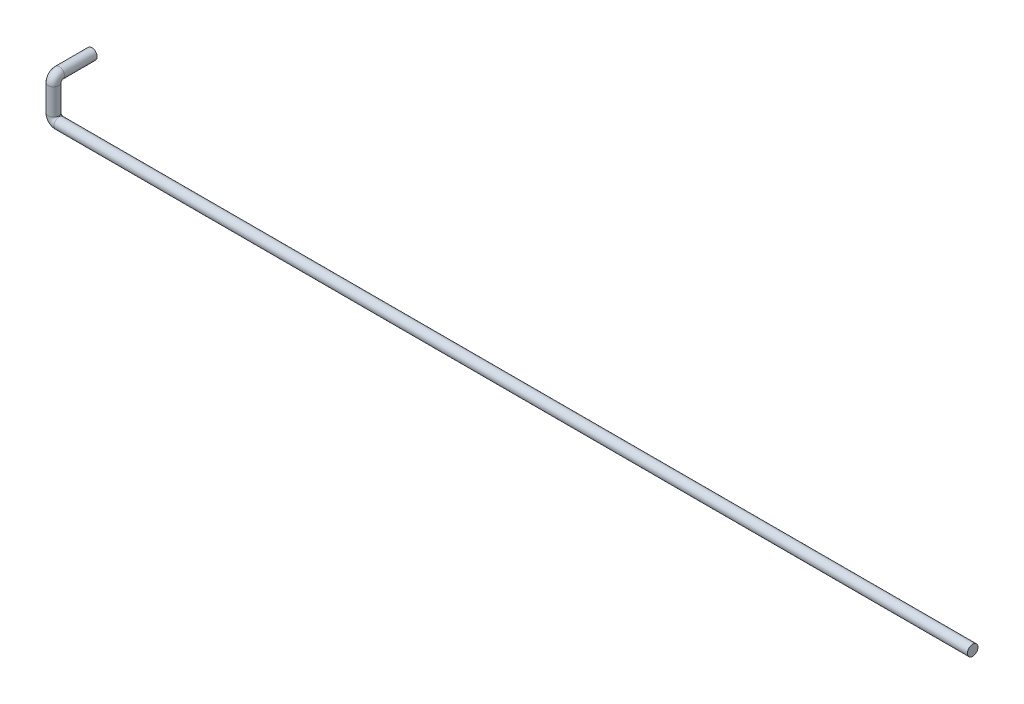
SolidWorks part; units mm, degrees
ref_plane "Alzado" through (0, 0, 0) normal (0, 0, 1) x (1, 0, 0)
ref_plane "Planta" through (0, 0, 0) normal (0, 1, 0) x (1, 0, 0)
ref_plane "Vista lateral" through (0, 0, 0) normal (1, 0, 0) x (0, 0, -1)
sketch3d "Croquis3D1"
  line L0 (0, 0, 0) -> (-2374, 0, 0)
  line L1 (-2389, 15, 0) -> (-2389, 83, 0)
  line L2 (-2389, 98, -15) -> (-2389, 98, -100)
  arc A0 (-2389, 83, 0) -> (-2389, 98, -15) centre (-2389, 83, -15) ccw
  arc A1 (-2374, 0, 0) -> (-2389, 15, 0) centre (-2374, 15, 0) ccw
  point P7 (-2389, 98, 0)
  point P8 (-2404, 83, -15)
  point P11 (-2389, 0, 0)
  point P12 (-2374, 15, -15)
  dimension "D4" = 15
  dimension "D1" = 2389
  dimension "D2" = 98
  dimension "D3" = 100
sketch "Croquis1" plane through (0, 0, 0) normal (1, 0, 0) x (0, 0, -1)
  circle A0 centre (0, 0) radius 13.7
  dimension "D1" = 27.4
sweep "Barrer1" add profiles "Croquis1" path "Croquis3D1"
